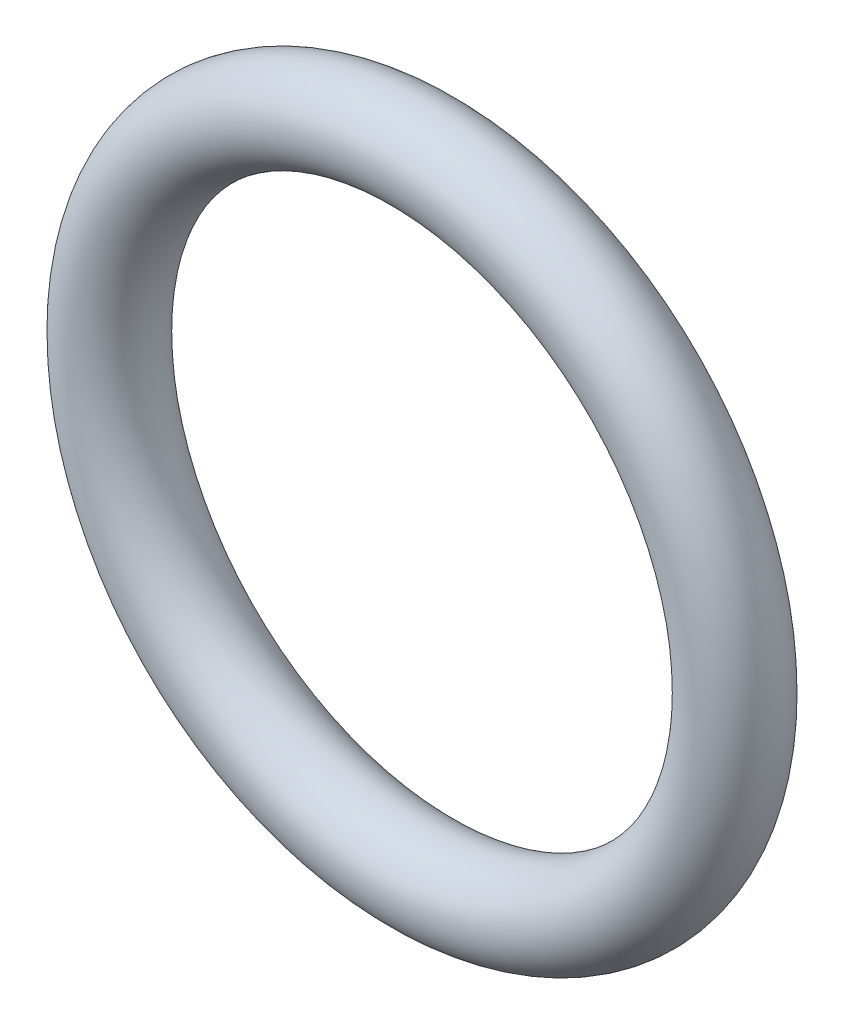
SolidWorks part; units mm, degrees
ref_plane "Front" through (0, 0, 0) normal (0, 0, 1) x (1, 0, 0)
ref_plane "Top" through (0, 0, 0) normal (0, 1, 0) x (1, 0, 0)
ref_plane "Right" through (0, 0, 0) normal (1, 0, 0) x (0, 0, -1)
sketch "Sketch1" plane through (0, 0, 0) normal (1, 0, 0) x (0, -1, 0)
  line L0 (0, -0.889) -> (0, 0.889) construction
  line L2 (-7.907, 0) -> (7.907, 0) construction
  line L3 (-5.4102, 0) -> (5.4102, 0) construction
  circle A0 centre (6.2992, 0) radius 0.889
  point P9 (5.4102, 0)
  point P10 (7.1882, 0)
  point P13 (6.2992, 0.889)
  point P14 (6.2992, -0.889)
  dimension "Width" = 1.778
  dimension "ID" = 10.8204
revolve "Revolve1" add sketch "Sketch1" angle 360 about L0
sketch "Sketch2" plane through (0, 0, 0) normal (0, 0, 1) x (1, 0, 0)
  circle A0 centre (0, 0) radius 4.4426
